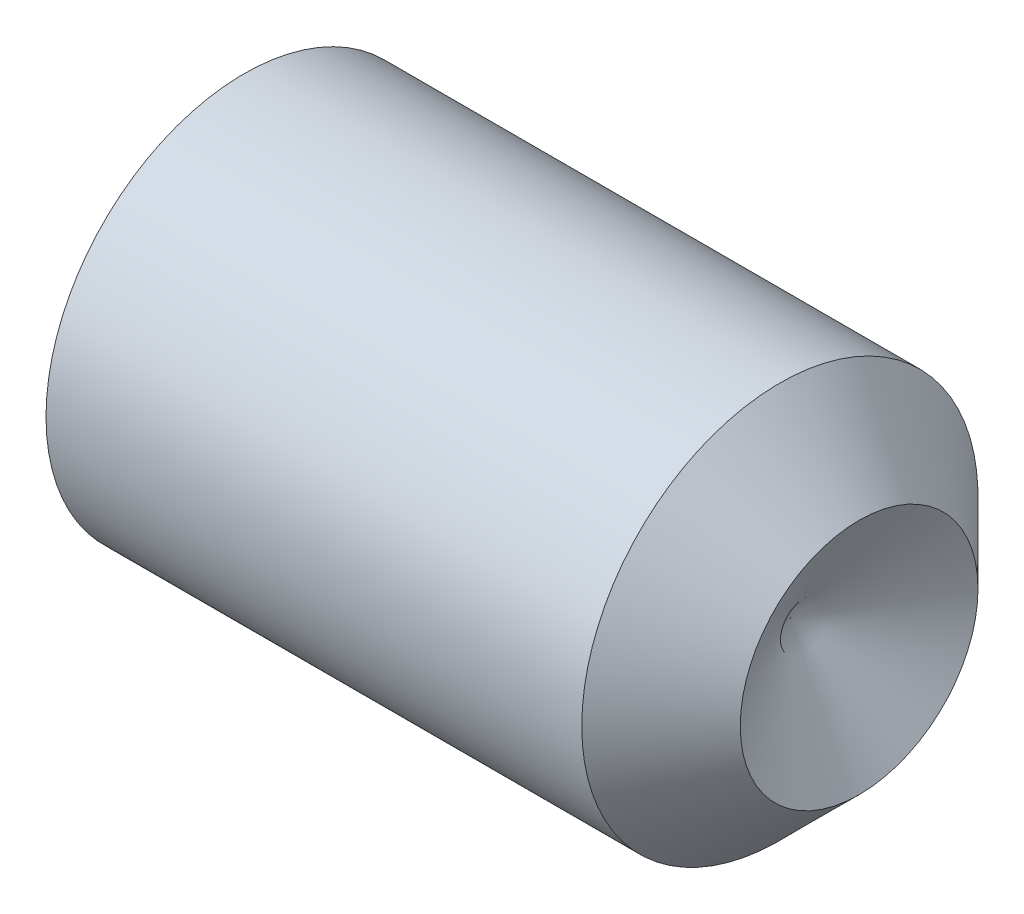
SolidWorks part; units mm, degrees
ref_plane "Plane1" through (0, 0, 0) normal (0, 0, 1) x (1, 0, 0)
ref_plane "Plane2" through (0, 0, 0) normal (0, 1, 0) x (1, 0, 0)
ref_plane "Plane3" through (0, 0, 0) normal (1, 0, 0) x (0, 0, -1)
sketch "BodySke" plane through (0, 0, 0) normal (0, 0, 1) x (1, 0, 0)
  line L0 (0, 0) -> (0, 4.172)
  line L1 (0, 4.172) -> (0.478, 5)
  line L2 (0.478, 5) -> (14, 5)
  line L3 (14, 5) -> (16, 3)
  line L4 (14.2679, 0) -> (0, 0)
  line L5 (-12.7, 0) -> (88.9, 0) construction
  line L6 (14.2679, 0) -> (16, 3)
  line L7 (16, 3) -> (16, 12.525) construction
  line L8 (0, -4.172) -> (0.478, -5) construction
  line L9 (14.2679, 0) -> (16, -3) construction
  line L10 (14, -5) -> (16, -3) construction
  line L11 (0.75, 15.875) -> (0.75, -3.175) construction
  dimension "Length" = 16
  dimension "Diameter" = 10
  dimension "Drive_ch_ang" = 60
  dimension "Minor_dia" = 8.344
  dimension "Cup_nose_ang" = 45
  dimension "Cup_ang" = 120
  dimension "Cup_dia" = 6
  dimension "Advance" = 1.5
revolve "BaseBody" add sketch "BodySke" angle 360 about L5
cosmetic thread "ThreadCosmetic" [suppressed] parameters "Thread_minor"=8.344
sketch "Sketch2" plane through (0, 0, 0) normal (-1, 0, 0) x (0, 0, 1)
  line L0 (1.4434, 2.5) -> (-1.4434, 2.5)
  line L1 (-1.4434, 2.5) -> (-2.8868, 0)
  line L2 (1.4434, 2.5) -> (2.8868, 0)
  line L3 (1.4434, -2.5) -> (2.8868, 0)
  line L4 (1.4434, -2.5) -> (-1.4434, -2.5)
  line L5 (-1.4434, -2.5) -> (-2.8868, 0)
  dimension "Hex_size" = 5
  dimension "D2" = 2.5
  dimension "D3" = 2.5
extrude "Hex" cut sketch "Sketch2" against normal blind 6
sketch "ThdSchSke" plane through (0, 0, 0) normal (0, 0, 1) x (1, 0, 0)
  line L0 (0.478, -4.172) -> (-0.1017, -5)
  line L1 (0.478, -4.172) -> (1.0578, -5)
  line L2 (1.0578, -5) -> (1.0578, -6.25)
  line L3 (-3.175, 0) -> (5.1513, 0) construction
  line L4 (0.478, 5) -> (0.478, -5) construction
  line L5 (1.0578, -6.25) -> (-0.1017, -6.25)
  line L6 (-0.1017, -6.25) -> (-0.1017, -5)
  dimension "Thread_minor" = 8.344
  dimension "Diameter" = 10
  dimension "SideAngle" = 55
  dimension "VeeAngle" = 70
  dimension "Overcut" = 12.5
revolve "ThreadSchematic" [suppressed] cut sketch "ThdSchSke" angle 360 about L3
pattern_linear "ThdSchPat" [suppressed]
equation "\"D2@Sketch2\" = \"Hex_size@Sketch2\" / 2"
equation "\"D3@Sketch2\" = \"Hex_size@Sketch2\" / 2"
equation "\"Thread_minor@ThreadCosmetic\" = \"Minor_dia@BodySke\""
equation "\"Thread_minor@ThdSchSke\" = \"Thread_minor@ThreadCosmetic\""
equation "\"Diameter@ThdSchSke\" = \"Diameter@BodySke\""
equation "\"Overcut@ThdSchSke\" = \"Diameter@BodySke\" * 1.25"
equation "\"Num_threads@ThdSchPat\" = int( (\"Length@BodySke\" - ( ( ( \"Diameter@BodySke\" - \"Minor_dia@BodySke\" ) * 0.5 ) / tan( \"Drive_ch_ang@BodySke\" * 0.017453292 ) ) - ( ( ( \"Diameter@BodySke\" - \"Cup_dia@BodySke\" ) * 0.5 ) * tan( \"Cup_nose_ang@BodySke\" * 0.017453292 ) ) ) / \"Advance@BodySke\" + 0.999 )  + 1"
equation "\"Advance@ThdSchPat\" = (\"Length@BodySke\" - ( ( ( \"Diameter@BodySke\" - \"Minor_dia@BodySke\" ) * 0.5 ) / tan( \"Drive_ch_ang@BodySke\" * 0.017453292 ) ) - ( ( ( \"Diameter@BodySke\" - \"Cup_dia@BodySke\" ) * 0.5 ) * tan( \"Cup_nose_ang@BodySke\" * 0.017453292 ) ) ) /  (\"Num_threads@ThdSchPat\" - 1) 'relax it"
equation "' \"Num_threads@ThdSchPat\" = \"Num_threads@ThdSchPat\" - sgn( \"Num_threads@ThdSchPat\" - 1) '---chamfered tips only---"
